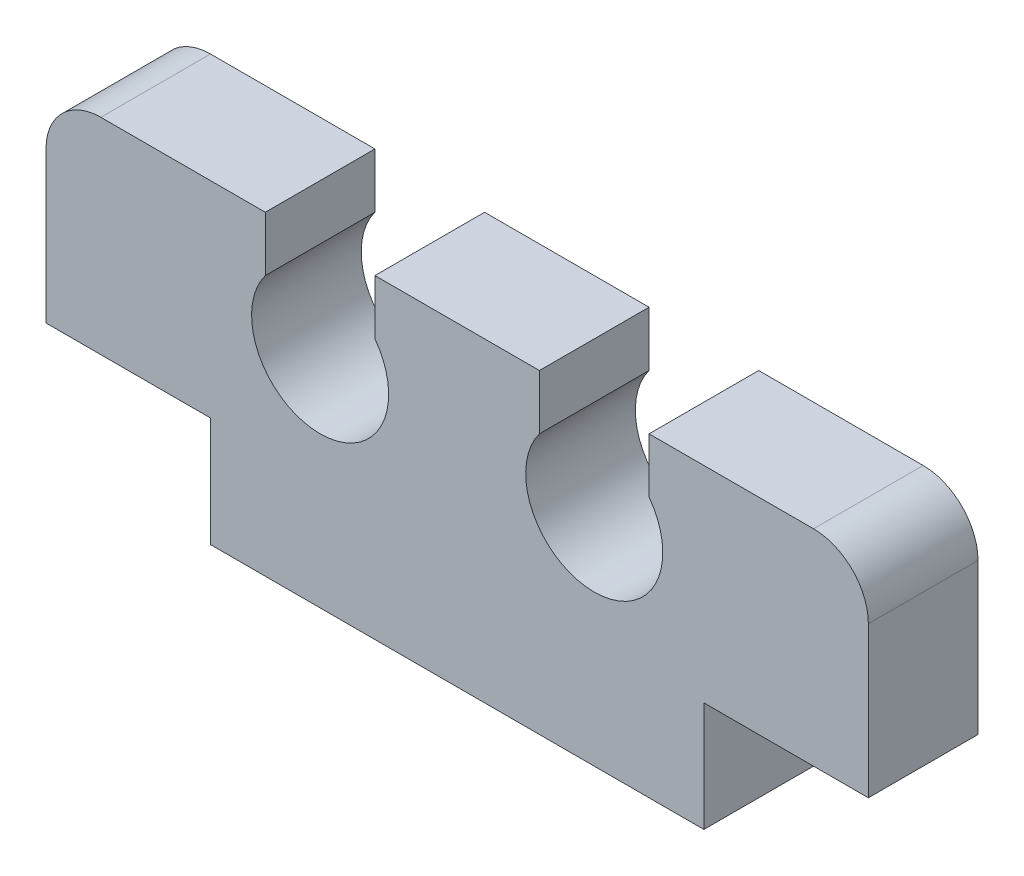
SolidWorks part; units mm, degrees
ref_plane "Front Plane" through (0, 0, 0) normal (0, 0, 1) x (1, 0, 0)
ref_plane "Top Plane" through (0, 0, 0) normal (0, 1, 0) x (1, 0, 0)
ref_plane "Right Plane" through (0, 0, 0) normal (1, 0, 0) x (0, 0, -1)
sketch "Sketch1" plane through (0, 0, 0) normal (0, 0, 1) x (1, 0, 0)
  line L14 (-4.5, 0) -> (4.5, 0)
  line L15 (-4.5, 0) -> (-4.5, 2)
  line L16 (-4.5, 2) -> (-7.5, 2)
  line L17 (-7.5, 2) -> (-7.5, 5.75)
  line L18 (-7.5, 5.75) -> (-3.5, 5.75)
  line L19 (0, 5.75) -> (0, 0) construction
  line L20 (-3.5, 4.75) -> (-3.5, 5.75)
  line L21 (-1.5, 4.75) -> (-1.5, 5.75)
  line L22 (-1.5, 5.75) -> (1.5, 5.75)
  line L23 (1.5, 4.75) -> (1.5, 5.75)
  line L24 (3.5, 4.75) -> (3.5, 5.75)
  line L25 (7.5, 5.75) -> (3.5, 5.75)
  line L26 (7.5, 2) -> (7.5, 5.75)
  line L27 (4.5, 2) -> (7.5, 2)
  line L28 (4.5, 0) -> (4.5, 2)
  arc A4 (-3.5, 4.75) -> (-1.5, 4.75) centre (-2.5, 4) ccw
  arc A5 (3.5, 4.75) -> (1.5, 4.75) centre (2.5, 4) cw
  dimension "D2" = 2.5
  dimension "D1" = 1.75
  dimension "D3" = 2
  dimension "D4" = 4.5
  dimension "D5" = 7.5
  dimension "D6" = 2
  dimension "D7" = 5.75
  dimension "D8" = 2.5
extrude "Tube Plate MCP Body" add sketch "Sketch1" along normal blind 2
fillet "Tube Plate MCP Contouring" radius 1 2 edges at (7.5, 5.75, 1) (-7.5, 5.75, 1)
equation "\"D7@Sketch1\"=\"rp@Parameters@RobotHandParameters.SLDPRT\" - 2 - \"Tjointp@Parameters@RobotHandParameters.SLDPRT\"/2 + 1.75mm"
